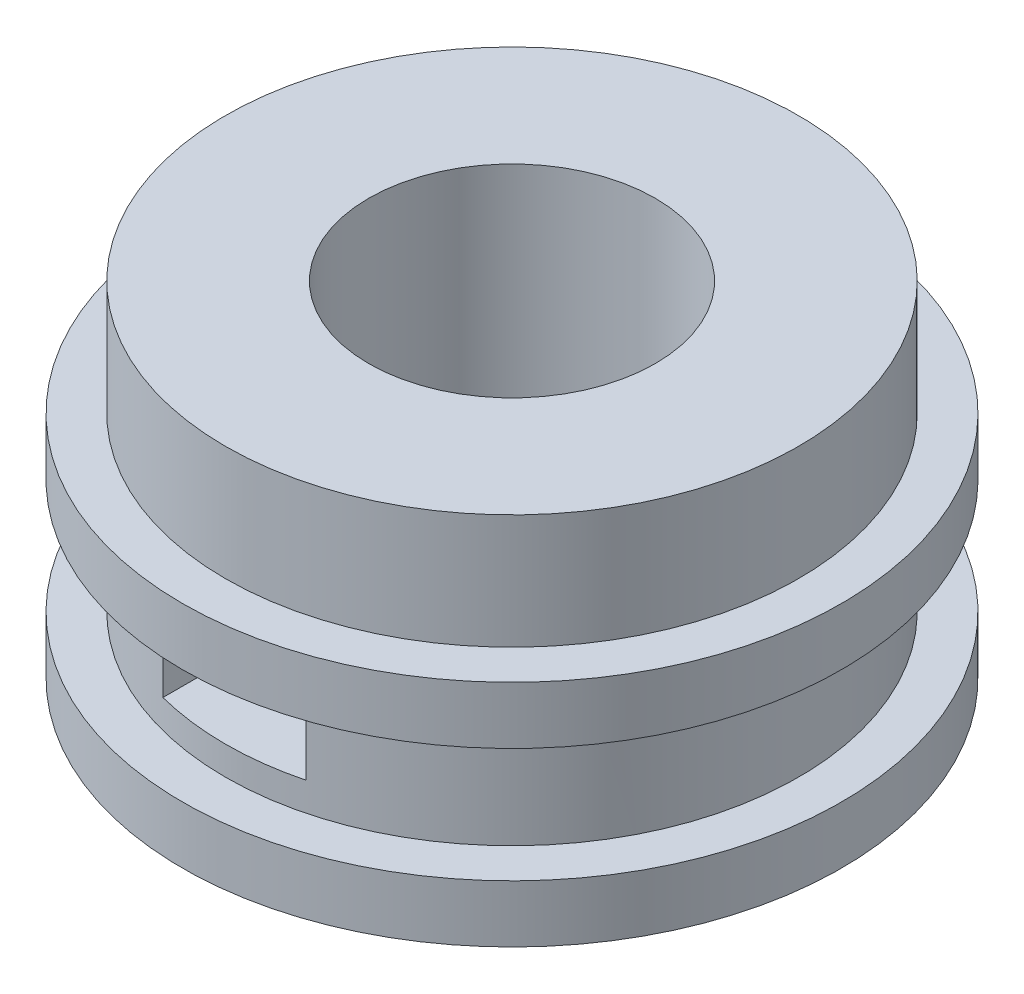
SolidWorks part; units mm, degrees
material "PLA Aero Bambu"
ref_plane "Front Plane" through (0, 0, 0) normal (0, 0, 1) x (1, 0, 0)
ref_plane "Top Plane" through (0, 0, 0) normal (0, 1, 0) x (1, 0, 0)
ref_plane "Right Plane" through (0, 0, 0) normal (1, 0, 0) x (0, 0, -1)
sketch "Sketch1" plane through (0, 0, 0) normal (0, 1, 0) x (1, 0, 0)
  circle A0 centre (0, 0) radius 2.5
  circle A1 centre (0, 0) radius 5
  dimension "D1" = 5
  dimension "D2" = 10
extrude "Boss-Extrude1" add sketch "Sketch1" along normal blind 4 and the other way blind 2
sketch "Sketch2" plane through (0, 0, 0) normal (0, 0, 1) x (1, 0, 0)
  line L1 (-1.25, 0.5) -> (1.25, 0.5)
  line L2 (-1.25, 0.5) -> (-1.25, -0.5)
  line L3 (-1.25, -0.5) -> (1.25, -0.5)
  line L4 (1.25, 0.5) -> (1.25, -0.5)
  point P4 (0, -0.5)
  point P6 (-1.25, 0)
  dimension "D1" = 1
  dimension "D2" = 2.5
extrude "Cut-Extrude1" cut sketch "Sketch2" against normal through all and the other way through all
sketch "Sketch3" plane through (0, -2, 0) normal (0, -1, 0) x (1, 0, 0)
  circle A0 centre (0, 0) radius 5
  circle A1 centre (0, 0) radius 5.75
  circle A2 centre (0, 0) radius 5 construction
  dimension "D1" = 11.5
extrude "Boss-Extrude2" add sketch "Sketch3" against normal blind 1
ref_plane "Plane1" through (0, 1, 0) normal (0, 1, 0) x (1, 0, 0)
sketch "Sketch5" plane through (0, 1, 0) normal (0, 1, 0) x (1, 0, 0)
  circle A0 centre (0, 0) radius 5.75
  circle A1 centre (0, 0) radius 5.75 construction
  circle A2 centre (0, 0) radius 5
  circle A4 centre (0, 0) radius 5 construction
extrude "Boss-Extrude3" add sketch "Sketch5" along normal blind 1
